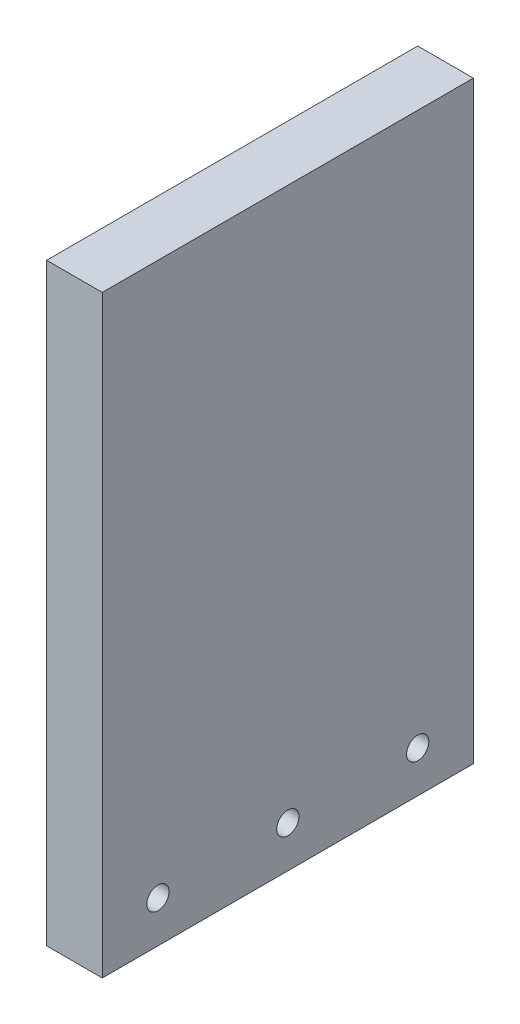
SolidWorks part; units mm, degrees
ref_plane "Front Plane" through (0, 0, 0) normal (0, 0, 1) x (1, 0, 0)
ref_plane "Top Plane" through (0, 0, 0) normal (0, 1, 0) x (1, 0, 0)
ref_plane "Right Plane" through (0, 0, 0) normal (1, 0, 0) x (0, 0, -1)
sketch "Sketch1" plane through (0, 0, 0) normal (0, 1, 0) x (1, 0, 0)
  line L1 (0, 0) -> (19.05, 0)
  line L2 (0, 0) -> (0, 127)
  line L3 (0, 127) -> (19.05, 127)
  line L4 (19.05, 0) -> (19.05, 127)
  dimension "D1" = 19.05
  dimension "D2" = 127
extrude "Boss-Extrude2" add sketch "Sketch1" along normal blind 203.2
sketch "Sketch2" plane through (0, 0, 0) normal (-1, 0, 0) x (0, 0, 1)
  line L0 (-127, 0) -> (0, 0) construction
  line L1 (-127, 203.2) -> (-127, 0) construction
  circle A0 centre (-107.95, 14.224) radius 3.81
  circle A1 centre (-63.5, 14.224) radius 3.81
  circle A2 centre (-19.05, 14.224) radius 3.81
  dimension "D1" = 7.62
  dimension "D2" = 7.62
  dimension "D3" = 7.62
  dimension "D4" = 44.45
  dimension "D5" = 44.45
  dimension "D6" = 14.224
  dimension "D7" = 19.05
extrude "Cut-Extrude1" cut sketch "Sketch2" against normal blind 88.138
equation "\"LengthOfFront\"= ( \"Length Desired@Drivetrain.SLDASM\" / 2 ) - ( \"LengthOfCutOut\" / 2 )"
equation "\"LengthOfCutOut\"= \"LengthOfCutOut@Drivetrain.Assembly\""
equation "\"D1@Boss-Extrude2\"=\"LengthOfFront\""
